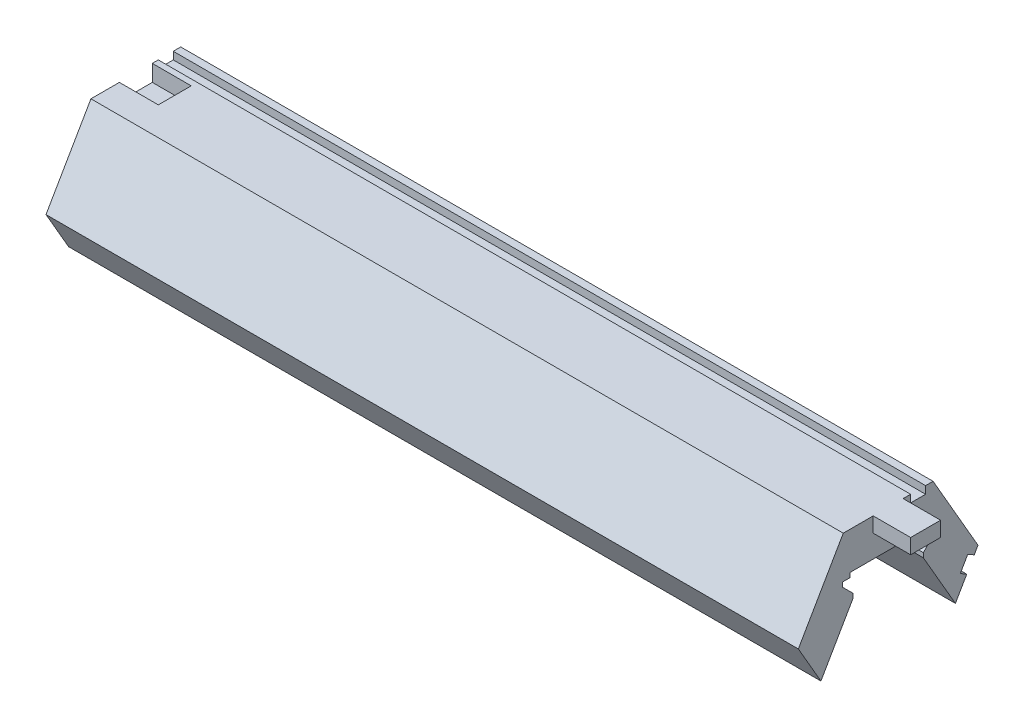
SolidWorks part; units mm, degrees
ref_plane "Front Plane" through (0, 0, 0) normal (0, 0, 1) x (1, 0, 0)
ref_plane "Top Plane" through (0, 0, 0) normal (0, 1, 0) x (1, 0, 0)
ref_plane "Right Plane" through (0, 0, 0) normal (1, 0, 0) x (0, 0, -1)
sketch "Master Design Profile" plane through (0, 0, 0) normal (1, 0, 0) x (0, 0, -1)
  line L0 (-5.1, 5.3923) -> (5.1, 5.3923)
  line L1 (12, 0) -> (6, 10.3923)
  line L2 (6, 10.3923) -> (-6, 10.3923)
  line L3 (-6, 10.3923) -> (-12, 0)
  line L4 (-12, 0) -> (-8.9829, -5.2258)
  line L5 (0, -10.3923) -> (6, -10.3923) construction
  line L6 (8.9829, -5.2258) -> (12, 0)
  line L7 (-5.1, 5.3923) -> (-5.1, 4.7923)
  line L8 (-5.1, 4.7923) -> (-6.1, 4.7923)
  line L9 (0, -28.6883) -> (0, 28.6883) construction
  line L10 (-6.1, 4.7923) -> (-6.1, 4.1923)
  line L11 (-6.1, 4.1923) -> (-4.7, 2.7923)
  line L13 (-4.7, 2.7923) -> (-4.7, 2.1923)
  line L14 (-4.7, 2.1923) -> (-8.9829, -5.2258)
  line L15 (4.7, 2.1923) -> (8.9829, -5.2258)
  line L16 (4.7, 2.7923) -> (4.7, 2.1923)
  line L17 (6.1, 4.1923) -> (4.7, 2.7923)
  line L18 (6.1, 4.7923) -> (6.1, 4.1923)
  line L19 (5.1, 4.7923) -> (6.1, 4.7923)
  line L20 (5.1, 5.3923) -> (5.1, 4.7923)
  line L21 (-9, -5.1962) -> (-6, -10.3923) construction
  line L22 (-8.9829, -5.2258) -> (-9, -5.1962) construction
  line L23 (-6, -10.3923) -> (0, -10.3923) construction
  line L24 (6, -10.3923) -> (9, -5.1962) construction
  line L25 (9, -5.1962) -> (8.9829, -5.2258) construction
  circle A0 centre (0, 0) radius 10.3923 construction
  point P15 (0, 0)
  point P16 (0, 5.3923)
  dimension "D1" = 10.2
  dimension "D2" = 0.6
  dimension "D3" = 0.6
  dimension "D4" = 1
  dimension "D5" = 135
  dimension "D6" = 2
  dimension "D7" = 5
  dimension "D8" = 210
  dimension "D9" = 0.6
  dimension "D10" = 12
sketch "LED Groove Profile Test" plane through (0, 0, 0) normal (1, 0, 0) x (0, 0, -1)
  line L0 (4.7, 2.7923) -> (4.7, 2.1923) construction
  line L1 (6.1, 4.1923) -> (4.7, 2.7923) construction
  line L2 (6.1, 4.7923) -> (6.1, 4.1923) construction
  line L3 (5.1, 4.7923) -> (6.1, 4.7923) construction
  line L4 (5.1, 5.3923) -> (5.1, 4.7923) construction
  line L5 (-5.1, 5.3923) -> (5.1, 5.3923) construction
  line L6 (-5.1, 5.3923) -> (-5.1, 4.7923) construction
  line L7 (-5.1, 4.7923) -> (-6.1, 4.7923) construction
  line L8 (-6.1, 4.7923) -> (-6.1, 4.1923) construction
  line L9 (-6.1, 4.1923) -> (-4.7, 2.7923) construction
  line L10 (-4.7, 2.7923) -> (-4.7, 2.1923) construction
  line L11 (-4.7, 2.7923) -> (-4.7, 2.1923)
  line L12 (-6.1, 4.1923) -> (-4.7, 2.7923)
  line L13 (-6.1, 4.7923) -> (-6.1, 4.1923)
  line L14 (-5.1, 4.7923) -> (-6.1, 4.7923)
  line L15 (-5.1, 5.3923) -> (-5.1, 4.7923)
  line L16 (-5.1, 5.3923) -> (5.1, 5.3923)
  line L17 (5.1, 5.3923) -> (5.1, 4.7923)
  line L18 (5.1, 4.7923) -> (6.1, 4.7923)
  line L19 (6.1, 4.7923) -> (6.1, 4.1923)
  line L20 (6.1, 4.1923) -> (4.7, 2.7923)
  line L21 (4.7, 2.7923) -> (4.7, 2.1923)
  line L22 (-4.7, 2.1923) -> (-7.5, 2.1923)
  line L23 (-7.5, 2.1923) -> (-7.5, 7.1923)
  line L24 (-7.5, 7.1923) -> (7.5, 7.1923)
  line L25 (7.5, 7.1923) -> (7.5, 2.1923)
  line L26 (7.5, 2.1923) -> (4.7, 2.1923)
  line L27 (0, -28.6883) -> (0, 28.6883) construction
  point P0 (0, 7.1923)
  dimension "D1" = 5
  dimension "D2" = 15
extrude "Boss-Extrude1" [suppressed] add sketch "LED Groove Profile Test" along normal mid plane 15
sketch "LED Segment" plane through (0, 0, 0) normal (1, 0, 0) x (0, 0, -1)
  line L0 (8.9829, -5.2258) -> (12, 0) construction
  line L1 (12, 0) -> (6, 10.3923) construction
  line L2 (6, 10.3923) -> (-6, 10.3923) construction
  line L3 (-6, 10.3923) -> (-12, 0) construction
  line L4 (-12, 0) -> (-8.9829, -5.2258) construction
  line L5 (-4.7, 2.1923) -> (-8.9829, -5.2258) construction
  line L6 (4.7, 2.1923) -> (8.9829, -5.2258) construction
  line L7 (4.7, 2.7923) -> (4.7, 2.1923) construction
  line L8 (6.1, 4.1923) -> (4.7, 2.7923) construction
  line L9 (6.1, 4.7923) -> (6.1, 4.1923) construction
  line L10 (5.1, 4.7923) -> (6.1, 4.7923) construction
  line L11 (5.1, 5.3923) -> (5.1, 4.7923) construction
  line L12 (-5.1, 5.3923) -> (5.1, 5.3923) construction
  line L13 (-5.1, 5.3923) -> (-5.1, 4.7923) construction
  line L14 (-5.1, 4.7923) -> (-6.1, 4.7923) construction
  line L15 (-6.1, 4.7923) -> (-6.1, 4.1923) construction
  line L16 (-4.7, 2.7923) -> (-4.7, 2.1923) construction
  line L17 (-6.1, 4.1923) -> (-4.7, 2.7923) construction
  line L18 (8.9829, -5.2258) -> (12, 0)
  line L19 (12, 0) -> (6, 10.3923)
  line L20 (6, 10.3923) -> (-6, 10.3923)
  line L21 (-6, 10.3923) -> (-12, 0)
  line L22 (-12, 0) -> (-8.9829, -5.2258)
  line L23 (-4.7, 2.1923) -> (-8.9829, -5.2258)
  line L24 (4.7, 2.1923) -> (8.9829, -5.2258)
  line L25 (4.7, 2.7923) -> (4.7, 2.1923)
  line L26 (6.1, 4.1923) -> (4.7, 2.7923)
  line L27 (6.1, 4.7923) -> (6.1, 4.1923)
  line L28 (5.1, 4.7923) -> (6.1, 4.7923)
  line L29 (5.1, 5.3923) -> (5.1, 4.7923)
  line L30 (-5.1, 5.3923) -> (5.1, 5.3923)
  line L31 (-5.1, 5.3923) -> (-5.1, 4.7923)
  line L32 (-5.1, 4.7923) -> (-6.1, 4.7923)
  line L33 (-6.1, 4.7923) -> (-6.1, 4.1923)
  line L34 (-4.7, 2.7923) -> (-4.7, 2.1923)
  line L35 (-6.1, 4.1923) -> (-4.7, 2.7923)
extrude "Boss-Extrude2" add sketch "LED Segment" along normal mid plane 100.5
sketch "Sketch3" plane through (50.25, 0, 0) normal (1, 0, 0) x (0, 0, -1)
  line L5 (5, 10.3923) -> (5, 9.3923)
  line L11 (6, 10.3923) -> (-6, 10.3923) construction
  line L12 (5, 9.3923) -> (3, 9.3923)
  line L13 (3, 9.3923) -> (3, 10.3923)
  line L14 (3, 10.3923) -> (5, 10.3923)
  line L15 (12, 0) -> (6, 10.3923) construction
  line L16 (12, 0) -> (6, 10.3923) construction
  line L17 (11.6944, 6.7518) -> (6.3056, 3.6405) construction
  line L18 (10.5, -2.5981) -> (11.5, -0.866)
  line L19 (9.634, -2.0981) -> (10.5, -2.5981)
  line L20 (10.634, -0.366) -> (9.634, -2.0981)
  line L21 (11.5, -0.866) -> (10.634, -0.366)
  point P12 (9, 5.1962)
  dimension "D1" = 1
  dimension "D2" = 1
  dimension "D3" = 2
extrude "Cut-Extrude2" cut sketch "Sketch3" against normal through all
sketch "Sketch4" plane through (50.25, 0, 0) normal (1, 0, 0) x (0, 0, -1)
  line L0 (3, 10.3923) -> (-6, 10.3923) construction
  line L1 (2, 10.3923) -> (-2, 10.3923)
  line L2 (2, 10.3923) -> (2, 8.3923)
  line L3 (2, 8.3923) -> (-2, 8.3923)
  line L4 (-2, 10.3923) -> (-2, 8.3923)
  line L5 (0, 10.3923) -> (0, 5.3923) construction
  line L6 (-5.1, 5.3923) -> (5.1, 5.3923) construction
  dimension "D1" = 4
  dimension "D2" = 2
extrude "Boss-Extrude3" add sketch "Sketch4" along normal blind 5
sketch "Sketch5" plane through (-50.25, 0, 0) normal (-1, 0, 0) x (0, 0, 1)
  line L1 (-2, 10.3923) -> (-2, 8.3923) construction
  line L2 (2, 8.3923) -> (2, 10.3923) construction
  line L3 (-2.2, 10.3923) -> (-2.2, 8.1923)
  line L4 (2, 10.3923) -> (-2, 10.3923)
  line L5 (2, 8.3923) -> (2, 10.3923)
  line L6 (-2, 8.3923) -> (2, 8.3923)
  line L7 (-2, 10.3923) -> (-2, 8.3923)
  line L8 (2, 10.3923) -> (-2, 10.3923)
  line L10 (-2, 8.3923) -> (2, 8.3923) construction
  line L11 (-2.2, 8.1923) -> (2.2, 8.1923)
  line L12 (2.2, 8.1923) -> (2.2, 10.3923)
  line L13 (-2, 10.3923) -> (-2.2, 10.3923)
  line L14 (2, 10.3923) -> (2.2, 10.3923)
  dimension "D1" = 0
  dimension "D2" = 0.2
extrude "Cut-Extrude3" cut sketch "Sketch5" against normal blind 5.2
